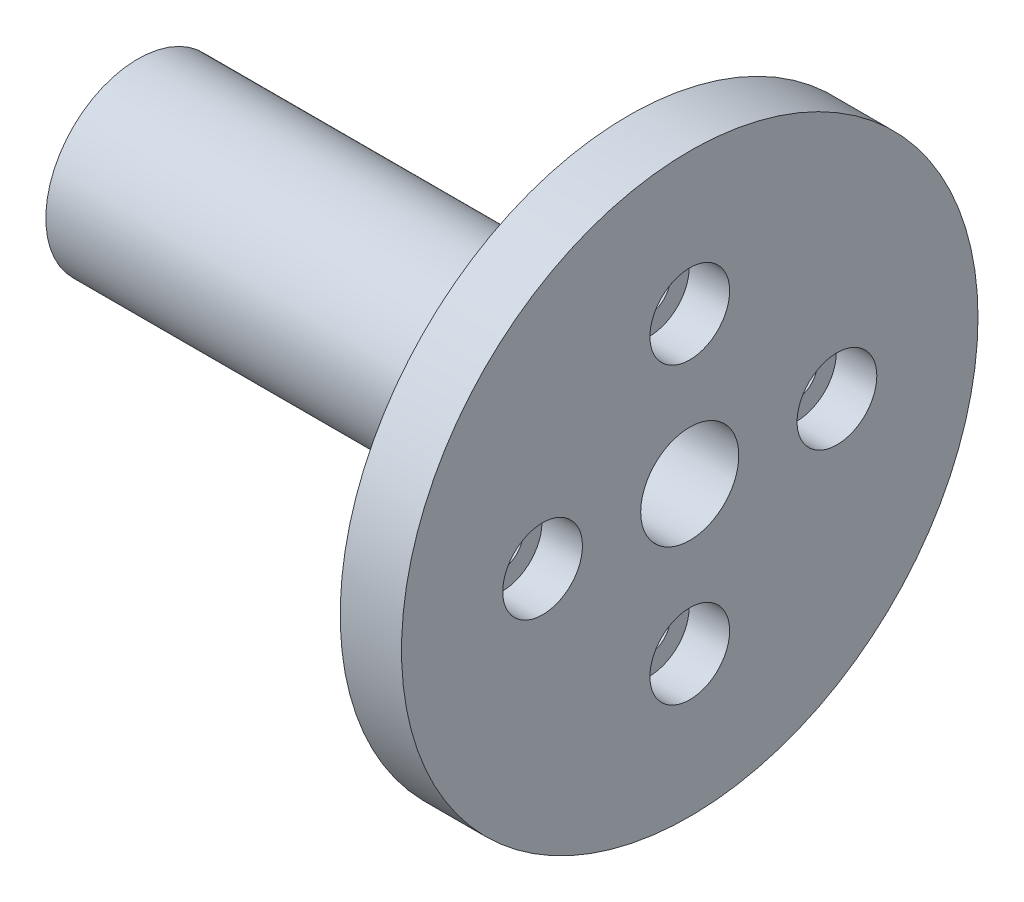
SolidWorks part; units mm, degrees
ref_plane "前视基准面" through (0, 0, 0) normal (0, 0, 1) x (1, 0, 0)
ref_plane "上视基准面" through (0, 0, 0) normal (0, 1, 0) x (1, 0, 0)
ref_plane "右视基准面" through (0, 0, 0) normal (1, 0, 0) x (0, 0, -1)
other "Configuration Table"
sketch "草图1" plane through (0, 0, 0) normal (0, 1, 0) x (1, 0, 0)
  line L0 (0, 0) -> (0, 16)
  line L1 (0, 16) -> (-5, 16)
  line L2 (-5, 16) -> (-5, 0)
  line L3 (-5, 0) -> (-45, 0)
  line L4 (-45, 0) -> (-45, -7.5)
  line L5 (0, 0) -> (0, -7.5)
  line L6 (0, -7.5) -> (-45, -7.5)
  dimension "D1" = 16
  dimension "D2" = 5
  dimension "D3" = 7.5
  dimension "D4" = 45
revolve "旋转1" add sketch "草图1" angle 360 about L6
sketch "草图2" plane through (-5, 0, 0) normal (-1, 0, 0) x (0, 0, 1)
  circle A0 centre (7.5, 0) radius 12 construction
  circle A1 centre (7.5, 12) radius 1.7
  circle A2 centre (19.5, 0) radius 1.7
  circle A3 centre (7.5, -12) radius 1.7
  circle A4 centre (-4.5, 0) radius 1.7
  dimension "D1" = 24
  dimension "D2" = 3.4
  dimension "D3" = 3.4
  dimension "D4" = 3.4
  dimension "D5" = 3.4
extrude "切除-拉伸1" cut sketch "草图2" against normal through all
sketch "草图3" plane through (0, 0, 0) normal (1, 0, 0) x (0, 0, -1)
  circle A0 centre (-7.5, 12) radius 3.25
  circle A1 centre (-19.5, 0) radius 3.25
  circle A2 centre (4.5, 0) radius 3.25
  circle A3 centre (-7.5, -12) radius 3.25
  dimension "D1" = 6.5
  dimension "D2" = 6.5
  dimension "D3" = 6.5
  dimension "D4" = 6.5
extrude "切除-拉伸2" cut sketch "草图3" against normal blind 3.3
sketch "草图4" plane through (-45, 0, 0) normal (-1, 0, 0) x (0, 0, 1)
  circle A0 centre (7.5, 0) radius 4
  dimension "D1" = 8
extrude "切除-拉伸3" cut sketch "草图4" against normal through all
sketch "Sketch2" plane through (0, 0, 0) normal (1, 0, 0) x (0, 0, -1)
  line L1 (-14.2, 20.8) -> (-0.8, 20.8)
  line L2 (-14.2, 20.8) -> (-14.2, 25.8)
  line L3 (-14.2, 25.8) -> (-0.8, 25.8)
  line L4 (-0.8, 20.8) -> (-0.8, 25.8)
  circle A1 centre (-7.5, 0) radius 4 construction
  point P6 (-7.5, 20.8)
  dimension "D1" = 20.8
  dimension "D2" = 13.4
  dimension "D3" = 5
